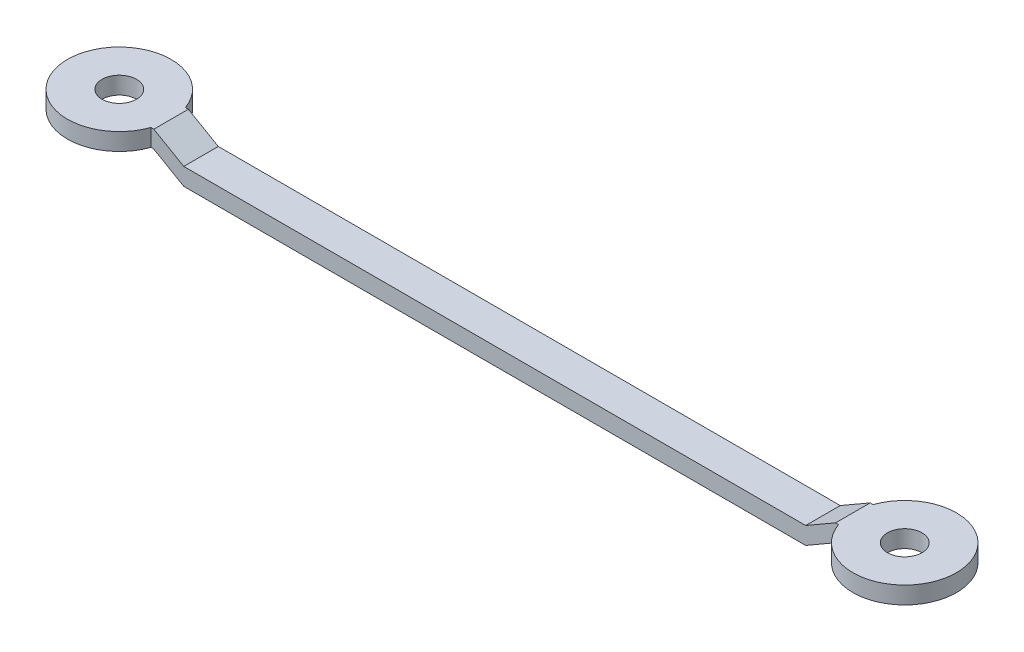
SolidWorks part; units mm, degrees
ref_plane "Front Plane" through (0, 0, 0) normal (0, 0, 1) x (1, 0, 0)
ref_plane "Top Plane" through (0, 0, 0) normal (0, 1, 0) x (1, 0, 0)
ref_plane "Right Plane" through (0, 0, 0) normal (1, 0, 0) x (0, 0, -1)
sketch "Sketch2" plane through (0, 0, 0) normal (0, 0, 1) x (1, 0, 0)
  line L0 (-18, 0) -> (18, 0)
  line L1 (18, 0) -> (19.7321, 1)
  line L2 (0, 0) -> (0, 1)
  line L3 (-18, 1) -> (18, 1)
  line L4 (18, 1) -> (19.7321, 2)
  line L5 (19.7321, 2) -> (20.9701, 2)
  line L6 (24.2857, 1) -> (9.6667, 1) construction
  line L7 (19.7321, 1) -> (20.9701, 1)
  line L8 (20.9701, 1) -> (20.9701, 2)
  line L9 (-19.7321, 1) -> (-20.9701, 1)
  line L10 (-19.7321, 2) -> (-20.9701, 2)
  line L11 (-18, 1) -> (-19.7321, 2)
  line L12 (-18, 0) -> (-19.7321, 1)
  line L13 (-20.9701, 1) -> (-20.9701, 2)
extrude "Boss-Extrude1" add sketch "Sketch2" along normal blind 2 contours L9 L13 L10 L11 L3 L4 L5 L8 L7 L1 L0 L12
sketch "Sketch3" plane through (0, 2, 0) normal (0, 1, 0) x (1, 0, 0)
  line L1 (-19.7321, -1) -> (-22.7321, -1)
  line L2 (-19.7321, -2) -> (-19.7321, 0) construction
  circle A1 centre (-22.7321, -1) radius 3
  dimension "D1" = 3
extrude "Boss-Extrude2" add sketch "Sketch3" against normal blind 1
sketch "Sketch4" plane through (0, 2, 0) normal (0, 1, 0) x (1, 0, 0)
  line L0 (19.7321, -1) -> (22.7321, -1)
  line L1 (19.7321, -2) -> (19.7321, 0) construction
  circle A0 centre (22.7321, -1) radius 3
  dimension "D2" = 6
  dimension "D1" = 3
extrude "Boss-Extrude3" add sketch "Sketch4" against normal blind 1 contours A0
sketch "Sketch5" plane through (0, 2, 0) normal (0, 1, 0) x (1, 0, 0)
  circle A0 centre (-22.7321, -1) radius 1
  circle A1 centre (22.7321, -1) radius 1
  point P6 (0, 0)
  point P7 (0, 0)
  point P8 (0, 0)
  point P9 (0, 0)
  dimension "D1" = 2
  dimension "D2" = 2
extrude "Cut-Extrude5" cut sketch "Sketch5" against normal through all and the other way through all
